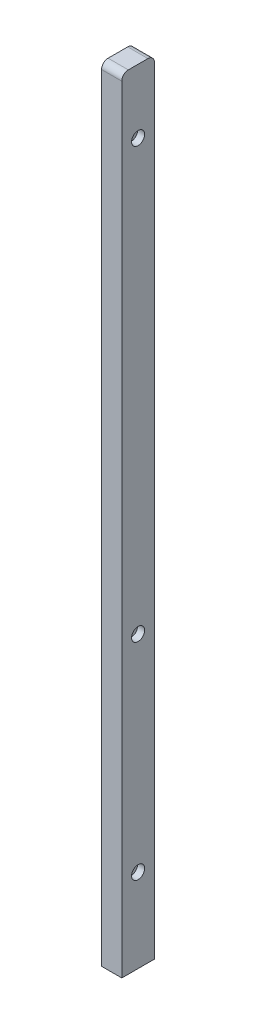
SolidWorks part; units mm, degrees
material "Cedar"
ref_plane "Front Plane" through (0, 0, 0) normal (0, 0, 1) x (1, 0, 0)
ref_plane "Top Plane" through (0, 0, 0) normal (0, 1, 0) x (1, 0, 0)
ref_plane "Right Plane" through (0, 0, 0) normal (1, 0, 0) x (0, 0, -1)
sketch "Sketch1" plane through (0, 0, 0) normal (0, 1, 0) x (1, 0, 0)
  line L1 (-7.75, -12.5) -> (7.75, -12.5)
  line L2 (-7.75, -12.5) -> (-7.75, 12.5)
  line L3 (-7.75, 12.5) -> (7.75, 12.5)
  line L4 (7.75, -12.5) -> (7.75, 12.5)
  line L5 (-7.75, -12.5) -> (7.75, 12.5) construction
  line L6 (-7.75, 12.5) -> (7.75, -12.5) construction
  point P0 (0, 0)
  dimension "D1" = 15.5
  dimension "D2" = 25
extrude "Boss-Extrude1" add sketch "Sketch1" along normal blind 600
fillet "Fillet1" radius 5 2 edges at (0, 600, -12.5) (0, 600, 12.5)
sketch "Sketch4" plane through (0, 0, 0) normal (0, -1, 0) x (-1, 0, 0)
  point P0 (0, 0)
hole_wizard "Ø5.0mm Dowel Hole1" positions "Sketch4" profile "Sketch3" hole size "Ø5.0" standard "ISO"
sketch "Sketch3" plane through (0, 0, 0) normal (1, 0, 0) x (0, 0, -1)
  line L0 (0, 0) -> (0, 13.9828)
  line L1 (0, 13.9828) -> (3.3, 12)
  line L2 (3.3, 12) -> (3.3, 0)
  line L5 (3.3, 0) -> (0, 0)
  line L10 (0, 13.9828) -> (-3.3, 12) construction
  line L11 (0, -6.35) -> (0, 107.95) construction
  dimension "Hole Dia." = 6.6
  dimension "Hole Depth" = 12
  dimension "Drill Angle" = 118
sketch "Sketch8" plane through (7.75, 0, 0) normal (1, 0, 0) x (0, 0, -1)
  line L0 (-12.5, 0) -> (12.5, 0) construction
  point P0 (0, 222)
  point P7 (0, 551)
  point P10 (0, 64)
  dimension "D1" = 222
  dimension "D2" = 551
  dimension "D3" = 64
hole_wizard "CBORE for M5 Hex Socket Head Cap Screw1" positions "Sketch8" profile "Sketch7" counterbore size "M5" standard "ISO" end condition through all
sketch "Sketch7" plane through (7.75, 222, 0) normal (0, 1, 0) x (0, 0, -1)
  line L0 (0, 0) -> (0, 15.5)
  line L1 (0, 15.5) -> (2.75, 15.5)
  line L3 (2.75, 15.5) -> (2.75, 5.4)
  line L4 (2.75, 5.4) -> (5, 5.4)
  line L5 (5, 5.4) -> (5, 0)
  line L7 (5, 0) -> (0, 0)
  line L11 (0, -6.35) -> (0, 107.95) construction
  dimension "Thru Hole Dia." = 5.5
  dimension "Thru Hole Depth" = 15.5
  dimension "C'Bore Dia." = 10
  dimension "C'Bore Depth" = 5.4
